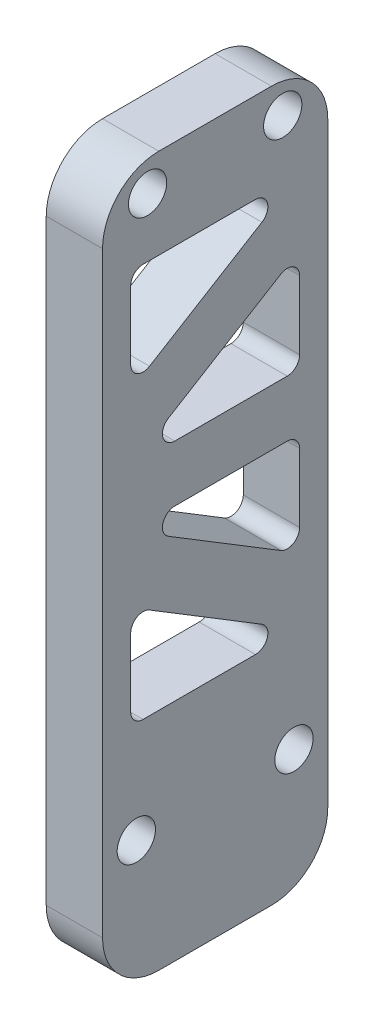
SolidWorks part; units mm, degrees
ref_plane "前视基准面" through (0, 0, 0) normal (0, 0, 1) x (1, 0, 0)
ref_plane "上视基准面" through (0, 0, 0) normal (0, 1, 0) x (1, 0, 0)
ref_plane "右视基准面" through (0, 0, 0) normal (1, 0, 0) x (0, 0, -1)
other "Configuration Table"
sketch "草图1" plane through (0, 0, 0) normal (1, 0, 0) x (0, 0, -1)
  line L1 (0, 0) -> (20, 0)
  line L2 (0, 0) -> (0, 63)
  line L3 (0, 63) -> (20, 63)
  line L4 (20, 0) -> (20, 63)
  dimension "D1" = 63
  dimension "D2" = 20
extrude "凸台-拉伸1" add sketch "草图1" along normal blind 5
hole_wizard "M3 间隙孔1" positions "草图2" profile "草图3" hole size "M3" standard "GB" end condition through all
sketch "草图2" plane through (5, 0, 0) normal (1, 0, 0) x (0, 0, -1)
  line L0 (0, 63) -> (0, 0) construction
  line L1 (20, 0) -> (20, 63) construction
  line L2 (0, 0) -> (20, 0) construction
  point P0 (3, 11)
  point P3 (17, 11)
  point P6 (16, 60.25)
  point P9 (4, 60.25)
  dimension "D1" = 4
  dimension "D2" = 4
  dimension "D3" = 60.25
  dimension "D4" = 60.25
sketch "草图3" plane through (5, 11, -3) normal (0, 1, 0) x (0, 0, -1)
  line L0 (0, 0) -> (0, 5)
  line L1 (0, 5) -> (1.7, 5)
  line L2 (1.7, 5) -> (1.7, 0)
  line L5 (1.7, 0) -> (0, 0)
  line L11 (0, -6.35) -> (0, 107.95) construction
  dimension "通孔孔直径" = 3.4
  dimension "通孔孔深度" = 5
fillet "圆角1" radius 5 4 edges at (2.5, 0, 0) (2.5, 0, -20) (2.5, 63, 0) (2.5, 63, -20)
sketch "草图4" plane through (5, 0, 0) normal (1, 0, 0) x (0, 0, -1)
  line L0 (15, 63) -> (5, 63) construction
  line L1 (17.5, 55) -> (2.5, 55)
  line L2 (17.5, 55) -> (17.5, 20)
  line L3 (17.5, 20) -> (2.5, 20)
  line L4 (2.5, 55) -> (2.5, 20)
  line L5 (12.75, 15) -> (22, 15) construction
  line L6 (20, 5) -> (20, 58) construction
  line L7 (0, 58) -> (0, 5) construction
  line L8 (17.5, 55) -> (2.5, 45.8558)
  line L9 (17.5, 49.1442) -> (2.5, 40)
  line L10 (2.5, 40) -> (17.5, 40)
  line L11 (2.5, 37.5) -> (17.5, 37.5) construction
  line L12 (2.5, 35) -> (17.5, 35)
  line L13 (17.5, 25.8558) -> (2.5, 35)
  line L14 (17.5, 20) -> (2.5, 29.1442)
  line L15 (17.5, 20) -> (2.5, 20)
  dimension "D1" = 8
  dimension "D2" = 5
  dimension "D3" = 2.5
  dimension "D4" = 2.5
  dimension "D5" = 2.5
  dimension "D6" = 5
extrude "切除-拉伸1" cut sketch "草图4" against normal blind 10 contours L8 L1 L4 | L9 L10 L2 | L13 L2 L12 | L3 L14 L4
fillet "圆角2" radius 1.1 12 edges at (2.5, 40, -17.5) (2.5, 40, -2.5) (2.5, 45.8558, -2.5) (2.5, 55, -2.5) (2.5, 55, -17.5) (2.5, 49.1442, -17.5) (2.5, 35, -17.5) (2.5, 25.8558, -17.5) (2.5, 35, -2.5) (2.5, 20, -2.5) (2.5, 20, -17.5) (2.5, 29.1442, -2.5)
